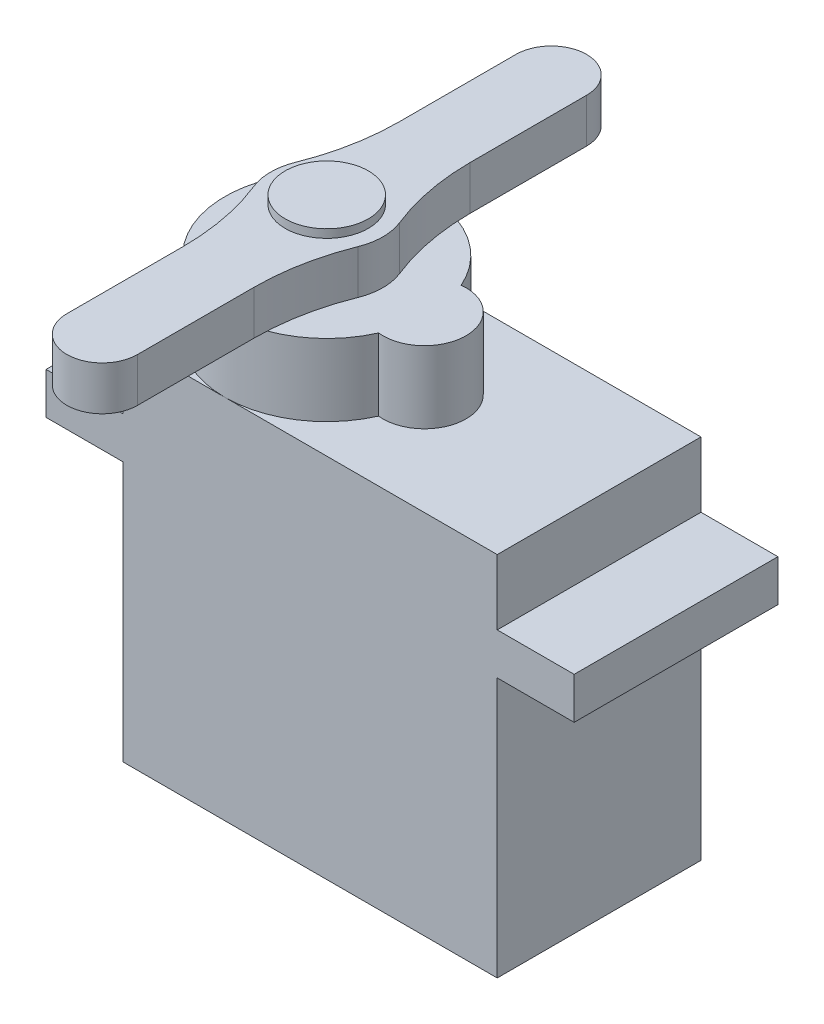
SolidWorks part; units mm, degrees
ref_plane "Front Plane" through (0, 0, 0) normal (0, 0, 1) x (1, 0, 0)
ref_plane "Top Plane" through (0, 0, 0) normal (0, 1, 0) x (1, 0, 0)
ref_plane "Right Plane" through (0, 0, 0) normal (1, 0, 0) x (0, 0, -1)
sketch "Sketch1" plane through (0, 0, 0) normal (0, 1, 0) x (1, 0, 0)
  line L1 (-11.43, 6.223) -> (11.43, 6.223)
  line L2 (-11.43, 6.223) -> (-11.43, -6.223)
  line L3 (-11.43, -6.223) -> (11.43, -6.223)
  line L4 (11.43, 6.223) -> (11.43, -6.223)
  point P4 (0, 6.223)
  point P5 (-11.43, 0)
  dimension "D1" = 22.86
  dimension "D2" = 12.446
extrude "Boss-Extrude1" add sketch "Sketch1" along normal blind 22.4
sketch "Sketch3" plane through (0, 0, 6.223) normal (0, 0, 1) x (1, 0, 0)
  line L0 (-11.43, 22.4) -> (-11.43, 0) construction
  line L1 (-16.129, 18.415) -> (-11.43, 18.415)
  line L2 (-16.129, 18.415) -> (-16.129, 15.875)
  line L3 (-16.129, 15.875) -> (-11.43, 15.875)
  line L4 (-11.43, 18.415) -> (-11.43, 15.875)
  line L5 (11.43, 22.4) -> (11.43, 0) construction
  line L6 (11.43, 18.415) -> (16.129, 18.415)
  line L7 (11.43, 18.415) -> (11.43, 15.875)
  line L8 (11.43, 15.875) -> (16.129, 15.875)
  line L9 (16.129, 18.415) -> (16.129, 15.875)
  line L11 (-11.43, 0) -> (11.43, 0) construction
  dimension "D1" = 32.258
  dimension "D2" = 2.54
  dimension "D3" = 18.415
extrude "Boss-Extrude3" add sketch "Sketch3" against normal up to surface (12.446 mm away) up to face at (0, 11.2, -6.223)
sketch "Sketch4" plane through (0, 22.4, 0) normal (0, 1, 0) x (1, 0, 0)
  line L0 (-11.43, 6.223) -> (-11.43, -6.223) construction
  line L1 (-11.43, -6.223) -> (11.43, -6.223) construction
  line L2 (11.43, 6.223) -> (-11.43, 6.223) construction
  arc A0 (0.481, 2.5244) -> (0.481, -2.5244) centre (-5.207, 0) ccw
  arc A1 (0.481, -2.5244) -> (0.481, 2.5244) centre (0.762, 0) ccw
  point P1 (3.302, 0)
  dimension "D1" = 5.08
  dimension "D2" = 14.732
extrude "Boss-Extrude4" add sketch "Sketch4" along normal offset from surface (4.4 mm away) 26.8 contours A0 A1 up to face at (0, 0, 0)
sketch "Sketch5" plane through (0, 26.8, 0) normal (0, 1, 0) x (1, 0, 0)
  circle A0 centre (-5.207, 0) radius 2.54
  arc A2 (0.481, 2.5244) -> (0.481, -2.5244) centre (-5.207, 0) ccw construction
  dimension "D1" = 5.08
extrude "Boss-Extrude5" add sketch "Sketch5" along normal offset from surface (3.2 mm away) 30 up to face at (0, 0, 0)
sketch "Sketch6" plane through (0, 26.8, 0) normal (0, 1, 0) x (1, 0, 0)
  line L0 (-7.366, 6.604) -> (-7.366, 13.716)
  line L1 (-3.048, 13.716) -> (-3.048, 6.604)
  line L2 (-7.366, -6.604) -> (-7.366, -13.716)
  line L3 (-3.048, -13.716) -> (-3.048, -6.604)
  arc A0 (-8.3914, 1.2718) -> (-8.3914, -1.2718) centre (-5.207, 0) ccw
  arc A2 (-7.366, 13.716) -> (-3.048, 13.716) centre (-5.207, 13.716) cw
  arc A3 (-7.366, -13.716) -> (-3.048, -13.716) centre (-5.207, -13.716) ccw
  arc A4 (-8.3914, -1.2718) -> (-7.366, -6.604) centre (-21.7424, -6.604) cw
  arc A5 (-2.0226, -1.2718) -> (-3.048, -6.604) centre (11.3284, -6.604) ccw
  arc A6 (-7.366, 6.604) -> (-8.3914, 1.2718) centre (-21.7424, 6.604) cw
  arc A7 (-3.048, 6.604) -> (-2.0226, 1.2718) centre (11.3284, 6.604) ccw
  arc A8 (-2.0226, -1.2718) -> (-2.0226, 1.2718) centre (-5.207, 0) ccw
  point P3 (-8.636, 0)
  point P4 (-1.778, 0)
  point P24 (-5.207, 15.875)
  point P25 (-5.207, -15.875)
  dimension "D1" = 31.75
  dimension "D2" = 4.318
  dimension "D3" = 7.112
  dimension "D4" = 6.858
extrude "Boss-Extrude6" add sketch "Sketch6" along normal offset from surface (2.692 mm away) 0.508 separate body up to face at (-5.207, 30, 2.54)
sketch "Sketch7" plane through (0, 0, 0) normal (0, -1, 0) x (1, 0, 0)
  line L0 (-11.43, -6.223) -> (-11.43, 6.223) construction
  line L1 (-11.43, -1.905) -> (-13.208, -1.905)
  line L2 (-11.43, -1.905) -> (-11.43, 1.905)
  line L3 (-11.43, 1.905) -> (-13.208, 1.905)
  line L4 (-13.208, -1.905) -> (-13.208, 1.905)
  line L5 (11.43, -6.223) -> (11.43, 6.223) construction
  point P6 (-13.208, 0)
  dimension "D1" = 3.81
  dimension "D2" = 24.638
extrude "Boss-Extrude7" add sketch "Sketch7" against normal blind 1.27 from offset 4.318 separate body
